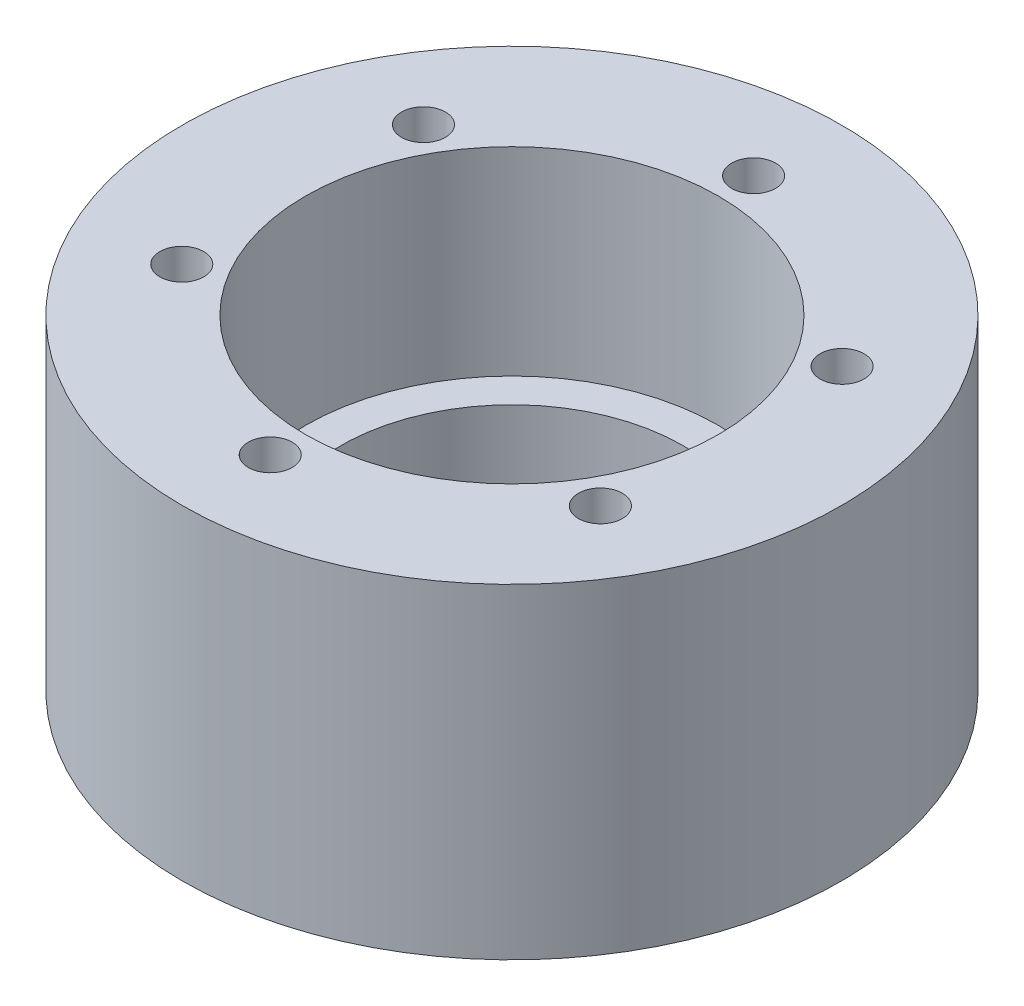
SolidWorks part; units mm, degrees
material "7075-T6 (SN)"
ref_plane "Front Plane" through (0, 0, 0) normal (0, 0, 1) x (1, 0, 0)
ref_plane "Top Plane" through (0, 0, 0) normal (0, 1, 0) x (1, 0, 0)
ref_plane "Right Plane" through (0, 0, 0) normal (1, 0, 0) x (0, 0, -1)
sketch "Sketch1" plane through (0, 0, 0) normal (0, 1, 0) x (1, 0, 0)
  circle A0 centre (0, 0) radius 37.5
  dimension "D1" = 75
extrude "Boss-Extrude1" add sketch "Sketch1" along normal blind 37
sketch "Sketch2" plane through (0, 37, 0) normal (0, 1, 0) x (1, 0, 0)
  circle A0 centre (0, 0) radius 23.5
  dimension "D1" = 47
extrude "Cut-Extrude1" cut sketch "Sketch2" against normal blind 22.6
sketch "Sketch3" plane through (0, 0, 0) normal (0, -1, 0) x (1, 0, 0)
  circle A0 centre (0, 0) radius 19.5
  dimension "D1" = 39
extrude "Cut-Extrude2" cut sketch "Sketch3" against normal through all
sketch "Sketch4" plane through (0, 37, 0) normal (0, 1, 0) x (1, 0, 0)
  circle A0 centre (0, 0) radius 27.5 construction
  point P1 (23.8157, 13.75)
  point P4 (0, 27.5)
  point P7 (23.8157, -13.75)
  point P11 (0, -27.5)
  point P12 (-23.8157, -13.75)
  point P13 (-23.8157, 13.75)
  dimension "D1" = 55
  dimension "D2" = 6
sketch "Sketch8" plane through (0, 0, 0) normal (0, -1, 0) x (1, 0, 0)
  circle A0 centre (0, 0) radius 31 construction
  point P3 (0, 31)
  point P4 (26.8468, 15.5)
  point P10 (26.8468, -15.5)
  point P11 (0, -31)
  point P12 (-26.8468, -15.5)
  point P13 (-26.8468, 15.5)
  dimension "D1" = 62
  dimension "D2" = 6
hole_wizard "M6x1.0 Tapped Hole1" positions "3DSketch4" profile "Sketch10" tap size "M6x1.0" standard "ANSI Metric"
sketch3d "3DSketch4"
  point P0 (0, 0, 31)
  point P3 (26.8468, 0, 15.5)
  point P6 (26.8468, 0, -15.5)
  point P9 (0, 0, -31)
  point P12 (-26.8468, 0, -15.5)
  point P15 (-26.8468, 0, 15.5)
sketch "Sketch10" plane through (0, 0, 31) normal (1, 0, 0) x (0, 0, -1)
  line L0 (0, 0) -> (0, 17.5022)
  line L1 (0, 17.5022) -> (2.5, 16)
  line L2 (2.5, 16) -> (2.5, 0)
  line L5 (2.5, 0) -> (0, 0)
  line L10 (0, 17.5022) -> (-2.5, 16) construction
  line L11 (0, -6.35) -> (0, 107.95) construction
  dimension "Tap Drill Dia." = 5
  dimension "Tap Drill Depth" = 16
  dimension "Drill Angle" = 118
cosmetic thread "Hole Thread5" parameters "D1"=15, "D2"=6
cosmetic thread "Hole Thread6" parameters "D1"=15, "D2"=6
cosmetic thread "Hole Thread7" parameters "D1"=15, "D2"=6
cosmetic thread "Hole Thread8" parameters "D1"=15, "D2"=6
cosmetic thread "Hole Thread9" parameters "D1"=15, "D2"=6
cosmetic thread "Hole Thread10" parameters "D1"=15, "D2"=6
hole_wizard "Tap Drill for M6x1.0 Tap1" positions "3DSketch5" profile "Sketch11" hole size "M6x1.0" standard "ANSI Metric"
sketch3d "3DSketch5"
  point P0 (0, 37, -27.5)
  point P4 (23.8157, 37, -13.75)
  point P7 (23.8157, 37, 13.75)
  point P10 (0, 37, 27.5)
  point P13 (-23.8157, 37, 13.75)
  point P16 (-23.8157, 37, -13.75)
sketch "Sketch11" plane through (0, 37, -27.5) normal (1, 0, 0) x (0, 0, 1)
  line L0 (0, 0) -> (0, 17.5022)
  line L1 (0, 17.5022) -> (2.5, 16)
  line L2 (2.5, 16) -> (2.5, 0)
  line L5 (2.5, 0) -> (0, 0)
  line L10 (0, 17.5022) -> (-2.5, 16) construction
  line L11 (0, -6.35) -> (0, 107.95) construction
  dimension "Hole Dia." = 5
  dimension "Hole Depth" = 16
  dimension "Drill Angle" = 118
